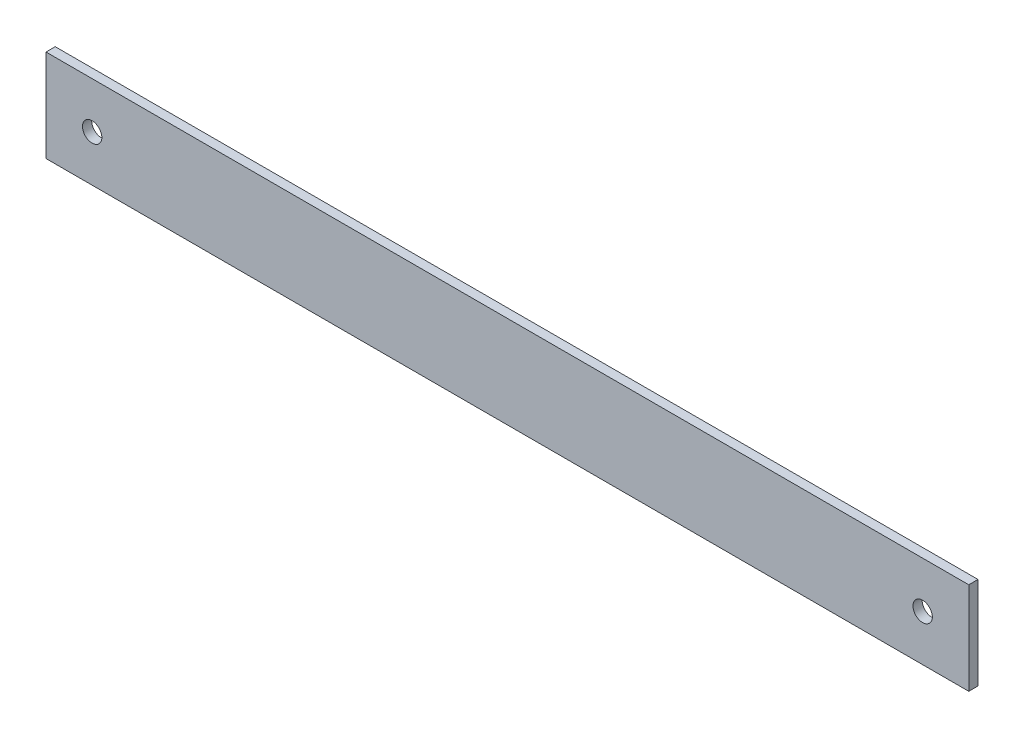
SolidWorks part; units mm, degrees
ref_plane "前视基准面" through (0, 0, 0) normal (0, 0, 1) x (1, 0, 0)
ref_plane "上视基准面" through (0, 0, 0) normal (0, 1, 0) x (1, 0, 0)
ref_plane "右视基准面" through (0, 0, 0) normal (1, 0, 0) x (0, 0, -1)
sketch "草图1" plane through (0, 0, 0) normal (0, 0, 1) x (1, 0, 0)
  line L1 (500, -50) -> (-500, -50)
  line L2 (500, -50) -> (500, 50)
  line L3 (500, 50) -> (-500, 50)
  line L4 (-500, -50) -> (-500, 50)
  line L5 (500, -50) -> (-500, 50) construction
  line L6 (500, 50) -> (-500, -50) construction
  point P0 (0, 0)
  dimension "D1" = 1000
  dimension "D2" = 100
extrude "凸台-拉伸1" add sketch "草图1" along normal mid plane 10
hole_wizard "M24 螺纹孔1" positions "草图3" profile "草图2" tap size "M24" standard "GB" end condition through all
sketch "草图3" plane through (0, 0, 5) normal (0, 0, 1) x (1, 0, 0)
  line L0 (500, -50) -> (500, 50) construction
  line L1 (-500, 50) -> (-500, -50) construction
  point P0 (-450, 0)
  point P2 (450, 0)
  dimension "D1" = 50
  dimension "D2" = 50
sketch "草图2" plane through (-450, 0, 5) normal (1, 0, 0) x (0, -1, 0)
  line L0 (0, 0) -> (0, 10)
  line L1 (0, 10) -> (10.5, 10)
  line L2 (10.5, 10) -> (10.5, 0)
  line L5 (10.5, 0) -> (0, 0)
  line L11 (0, -6.35) -> (0, 107.95) construction
  dimension "通孔螺纹孔钻头直径" = 21
  dimension "通孔螺纹孔钻头深度" = 10
cosmetic thread "孔螺蚊线1"
cosmetic thread "孔螺蚊线2"
